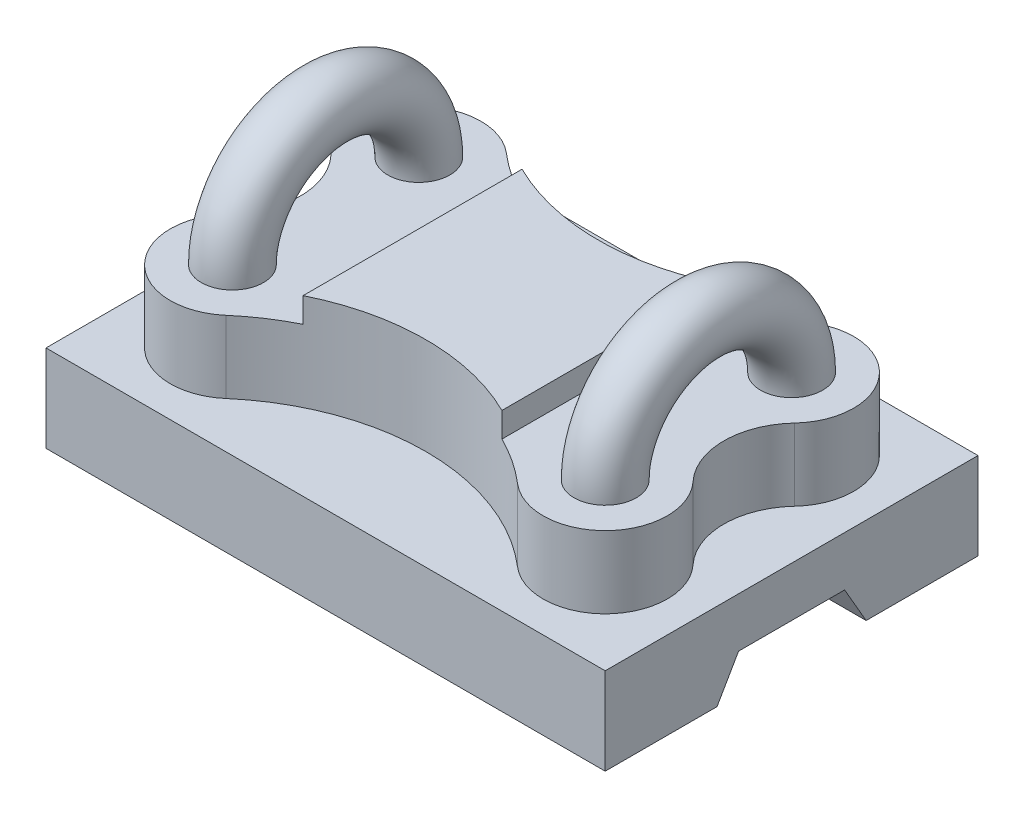
SolidWorks part; units mm, degrees
material "1060 Alloy"
ref_plane "Front Plane" through (0, 0, 0) normal (0, 0, 1) x (1, 0, 0)
ref_plane "Top Plane" through (0, 0, 0) normal (0, 1, 0) x (1, 0, 0)
ref_plane "Right Plane" through (0, 0, 0) normal (1, 0, 0) x (0, 0, -1)
sketch "Sketch1" plane through (0, 0, 0) normal (0, 1, 0) x (1, 0, 0)
  line L1 (-225, 150) -> (225, 150)
  line L2 (-225, 150) -> (-225, -150)
  line L3 (-225, -150) -> (225, -150)
  line L4 (225, 150) -> (225, -150)
  line L5 (-225, 150) -> (225, -150) construction
  line L6 (-225, -150) -> (225, 150) construction
  point P0 (0, 0)
  dimension "D1" = 300
  dimension "D2" = 450
extrude "Boss-Extrude1" add sketch "Sketch1" along normal blind 70
sketch "Sketch2" plane through (225, 0, 0) normal (1, 0, 0) x (0, 0, -1)
  line L0 (0, 0) -> (0, 66.644) construction
  line L1 (-60, 0) -> (-42.6795, 30)
  line L2 (-150, 0) -> (150, 0) construction
  line L3 (-42.6795, 30) -> (42.6795, 30)
  line L4 (60, 0) -> (42.6795, 30)
  line L5 (-60, 0) -> (60, 0)
  point P9 (0, 30)
  dimension "D1" = 60
  dimension "D2" = 120
  dimension "D3" = 30
extrude "Cut-Extrude1" cut sketch "Sketch2" against normal through all contours L5 L4 L3 L1
ref_plane "Plane1" through (0, 70, 0) normal (0, 1, 0) x (1, 0, 0)
sketch "Sketch3" plane through (0, 70, 0) normal (0, 1, 0) x (1, 0, 0)
  line L0 (-278.8274, 0) -> (280.2714, 0) construction
  line L1 (0, 167.9746) -> (0, -172.8363) construction
  line L2 (-80, 88.1108) -> (-80, -88.1108)
  line L3 (80, 88.1108) -> (80, -88.1108)
  line L5 (225, 150) -> (-225, 150) construction
  circle A0 centre (-150, 75) radius 25
  circle A1 centre (150, 75) radius 25
  circle A2 centre (150, -75) radius 25
  circle A3 centre (-150, -75) radius 25
  arc A4 (-117.3913, 112.9035) -> (-186.5761, 40.9091) centre (-150, 75) ccw
  arc A5 (117.3913, 112.9035) -> (186.5761, 40.9091) centre (150, 75) cw
  arc A6 (117.3913, -112.9035) -> (186.5761, -40.9091) centre (150, -75) ccw
  arc A7 (-117.3913, -112.9035) -> (-186.5761, -40.9091) centre (-150, -75) cw
  arc A8 (-186.5761, -40.9091) -> (-186.5761, 40.9091) centre (-230.4674, 0) ccw
  arc A9 (186.5761, -40.9091) -> (186.5761, 40.9091) centre (230.4674, 0) cw
  arc A10 (-117.3913, 112.9035) -> (117.3913, 112.9035) centre (0, 249.356) ccw
  arc A11 (-117.3913, -112.9035) -> (117.3913, -112.9035) centre (0, -249.356) cw
  dimension "D2" = 50
  dimension "D1" = 100
  dimension "D5" = 120
  dimension "D6" = 360
  dimension "D3" = 150
  dimension "D4" = 75
  dimension "D7" = 80
extrude "Boss-Extrude2" add sketch "Sketch3" along normal blind 58 contours A7 A11 L2 A10 A4 A8 A3 A0 | L2 A11 L3 A10 | L3 A11 A6 A9 A5 A10 A2 A1 | A0 | A3 | A2 | A1
ref_plane "Plane2" through (0, 128, 0) normal (0, 1, 0) x (1, 0, 0)
sketch "Sketch4" plane through (0, 128, 0) normal (0, 1, 0) x (1, 0, 0)
  line L0 (0, 82.551) -> (0, -101.6667) construction
  line L1 (-213.1685, 0) -> (216.6727, 0) construction
  line L2 (-80, 88.1108) -> (-80, -88.1108)
  line L3 (80, 88.1108) -> (80, -88.1108)
  arc A0 (-117.3913, 112.9035) -> (117.3913, 112.9035) centre (0, 249.356) ccw construction
  arc A1 (117.3913, -112.9035) -> (-117.3913, -112.9035) centre (0, -249.356) ccw construction
  arc A2 (80, -88.1108) -> (-80, -88.1108) centre (0, -249.356) ccw
  arc A3 (-80, 88.1108) -> (80, 88.1108) centre (0, 249.356) ccw
  dimension "D2" = 360
  dimension "D3" = 360
  dimension "D1" = 80
extrude "Boss-Extrude3" add sketch "Sketch4" along normal blind 20
sketch "Sketch5" plane through (0, 128, 0) normal (0, 1, 0) x (1, 0, 0)
  line L0 (0, 143.4005) -> (0, -150) construction
  line L1 (-225, -150) -> (225, -150) construction
  line L2 (-226.2092, 0) -> (225, 0) construction
  line L3 (225, -150) -> (225, 150) construction
  line L4 (225, 150) -> (-225, 150) construction
  circle A0 centre (-150, 75) radius 25
  circle A1 centre (150, 75) radius 25
  point P12 (0, 0)
  point P14 (-160.7701, 73.114)
  dimension "D1" = 50
  dimension "D2" = 75
  dimension "D3" = 150
revolve "Revolve1" add sketch "Sketch5" angle 180 about L2
